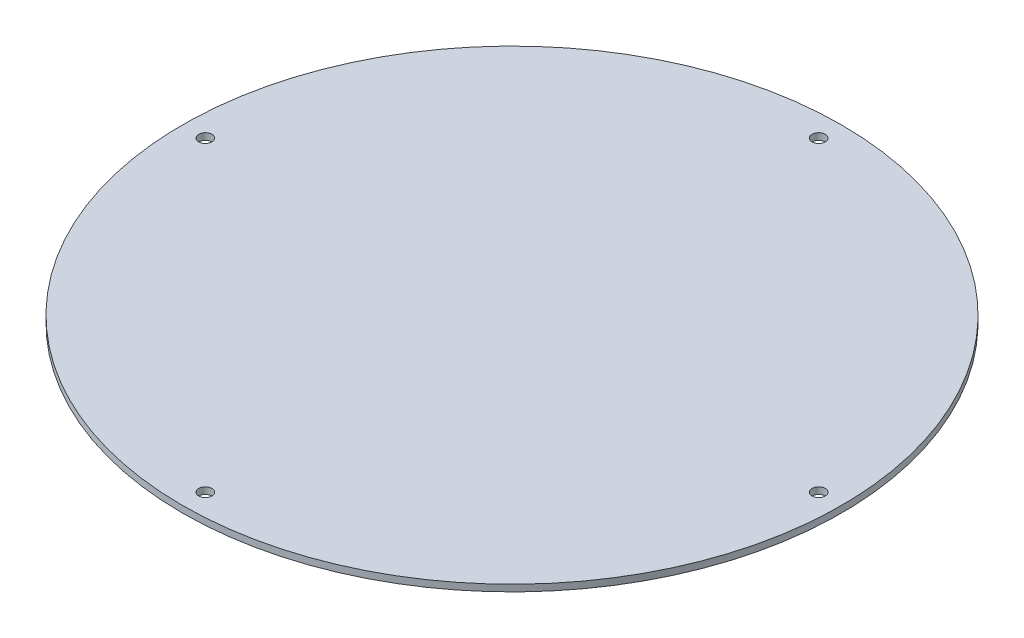
SolidWorks part; units mm, degrees
ref_plane "Front Plane" through (0, 0, 0) normal (0, 0, 1) x (1, 0, 0)
ref_plane "Top Plane" through (0, 0, 0) normal (0, 1, 0) x (1, 0, 0)
ref_plane "Right Plane" through (0, 0, 0) normal (1, 0, 0) x (0, 0, -1)
sketch "Sketch1" plane through (0, 0, 0) normal (0, 1, 0) x (1, 0, 0)
  circle A0 centre (0, 0) radius 81
extrude "Boss-Extrude1" add sketch "Sketch1" along normal blind 1.64
sketch "Sketch2" plane through (0, 1.64, 0) normal (0, 1, 0) x (1, 0, 0)
  line L0 (0, 0) -> (81, 0) construction
  line L1 (81, 0) -> (0, 0) construction
  line L2 (0, 0) -> (0, 81) construction
  line L3 (0, 81) -> (0, 0) construction
  line L4 (-81, 0) -> (0, 0) construction
  line L5 (0, -81) -> (0, 0) construction
  line L6 (-81, 0) -> (0, -81) construction
  line L7 (0, -81) -> (81, 0) construction
  line L8 (0, 81) -> (81, 0) construction
  line L9 (-81, 0) -> (0, 81) construction
  line L10 (-81, 0) -> (-77, 0) construction
  line L11 (0, 81) -> (0, 77) construction
  line L12 (81, 0) -> (77, 0) construction
  line L13 (0, -81) -> (0, -77) construction
  line L14 (0, -77) -> (0, -73.75) construction
  line L15 (-77, 0) -> (-73.75, 0) construction
  line L16 (0, 77) -> (0, 73.75) construction
  line L17 (77, 0) -> (73.75, 0) construction
  line L18 (0, -77) -> (0, -75.375)
  line L19 (77, 0) -> (75.375, 0)
  line L20 (-77, 0) -> (-75.375, 0)
  line L21 (0, 77) -> (0, 75.375)
  circle A0 centre (0, 0) radius 81 construction
  circle A1 centre (0, -75.375) radius 1.625
  circle A2 centre (-75.375, 0) radius 1.625
  circle A3 centre (0, 75.375) radius 1.625
  circle A4 centre (75.375, 0) radius 1.625
extrude "Cut-Extrude1" cut sketch "Sketch2" against normal through all
